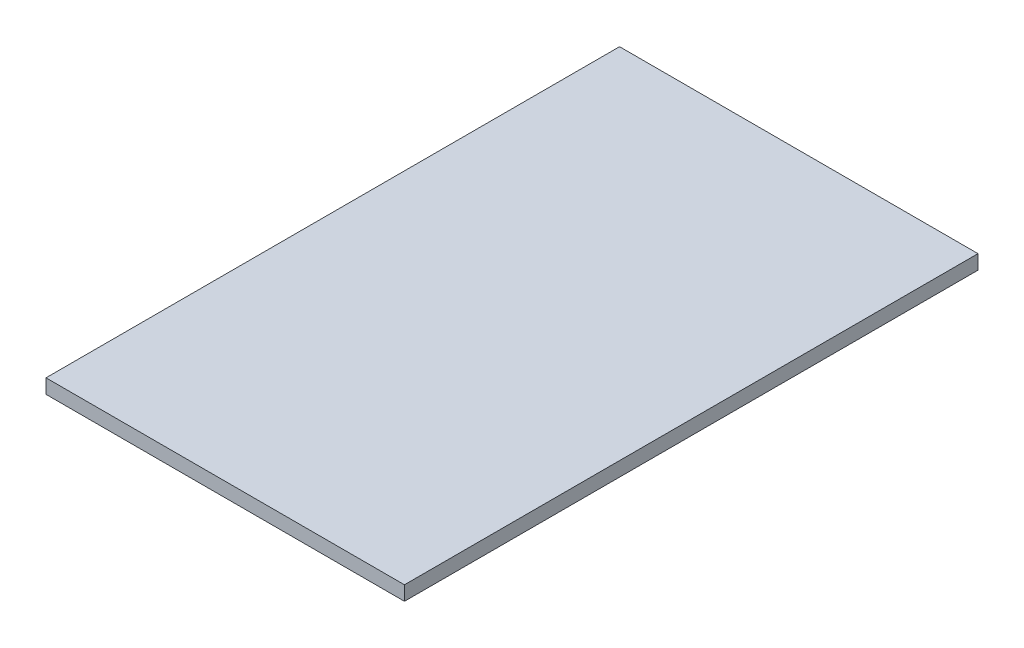
SolidWorks part; units mm, degrees
ref_plane "Front Plane" through (0, 0, 0) normal (0, 0, 1) x (1, 0, 0)
ref_plane "Top Plane" through (0, 0, 0) normal (0, 1, 0) x (1, 0, 0)
ref_plane "Right Plane" through (0, 0, 0) normal (1, 0, 0) x (0, 0, -1)
sketch "Sketch1" plane through (0, 0, 0) normal (0, 1, 0) x (1, 0, 0)
  line L1 (-25, -40) -> (25, -40)
  line L2 (-25, -40) -> (-25, 40)
  line L3 (-25, 40) -> (25, 40)
  line L4 (25, -40) -> (25, 40)
  line L5 (-25, -40) -> (25, 40) construction
  line L6 (-25, 40) -> (25, -40) construction
  point P0 (0, 0)
  dimension "D1" = 50
  dimension "D2" = 80
extrude "Boss-Extrude1" add sketch "Sketch1" along normal blind 2
